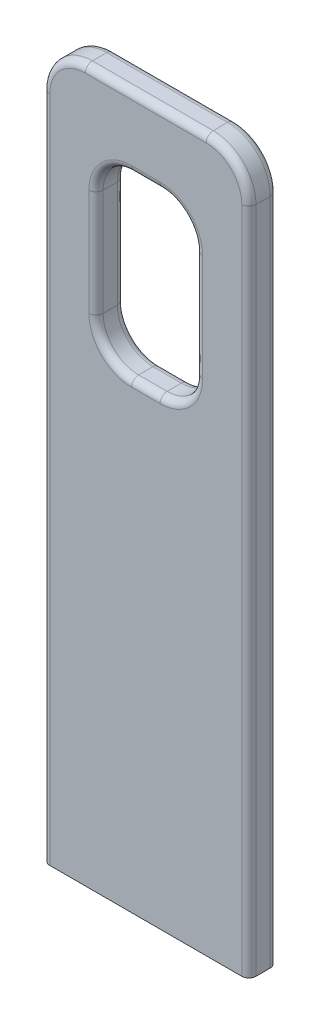
SolidWorks part; units mm, degrees
material "Copper"
ref_plane "Frontal" through (0, 0, 0) normal (0, 0, 1) x (1, 0, 0)
ref_plane "Superior" through (0, 0, 0) normal (0, 1, 0) x (1, 0, 0)
ref_plane "Direito" through (0, 0, 0) normal (1, 0, 0) x (0, 0, -1)
sketch "Sketch1" plane through (0, 0, 0) normal (0, 0, 1) x (1, 0, 0)
  line L0 (0, 9) -> (0, 10) construction
  line L1 (-1.45, 10) -> (1.45, 10)
  line L2 (-1.45, 10) -> (-1.45, 0)
  line L3 (-1.45, 0) -> (1.45, 0)
  line L4 (1.45, 10) -> (1.45, 0)
  line L5 (-0.7, 9) -> (0.7, 9)
  line L6 (-0.7, 9) -> (-0.7, 6.5)
  line L7 (-0.7, 6.5) -> (0.7, 6.5)
  line L8 (0.7, 9) -> (0.7, 6.5)
  dimension "D1" = 2.9
  dimension "D2" = 10
  dimension "D3" = 1.4
  dimension "D4" = 2.5
  dimension "D5" = 1
extrude "Extrude1" add sketch "Sketch1" along normal mid plane 0.4
fillet "Fillet1" radius 0.5 4 edges at (0.7, 6.5, 0) (0.7, 9, 0) (-0.7, 9, 0) (-0.7, 6.5, 0)
fillet "Fillet2" radius 0.6 2 edges at (1.45, 10, 0) (-1.45, 10, 0)
fillet "Fillet3" radius 0.1 26 edges at (-1.45, 4.7, -0.2) (-1.2743, 9.8243, -0.2) (0, 10, -0.2) (1.2743, 9.8243, -0.2) (-1.45, 4.7, 0.2) (-1.2743, 9.8243, 0.2) (0, 10, 0.2) (1.2743, 9.8243, 0.2) (1.45, 4.7, -0.2) (1.45, 4.7, 0.2) (-0.5536, 8.8536, 0.2) (0, 9, 0.2) (0.5536, 8.8536, 0.2) (0.7, 7.75, 0.2) (0.5536, 6.6464, 0.2) (0, 6.5, 0.2) (-0.5536, 6.6464, 0.2) (-0.5536, 8.8536, -0.2) (0, 9, -0.2) (0.5536, 8.8536, -0.2) (0.7, 7.75, -0.2) (0.5536, 6.6464, -0.2) (0, 6.5, -0.2) (-0.5536, 6.6464, -0.2) (-0.7, 7.75, 0.2) (-0.7, 7.75, -0.2)
